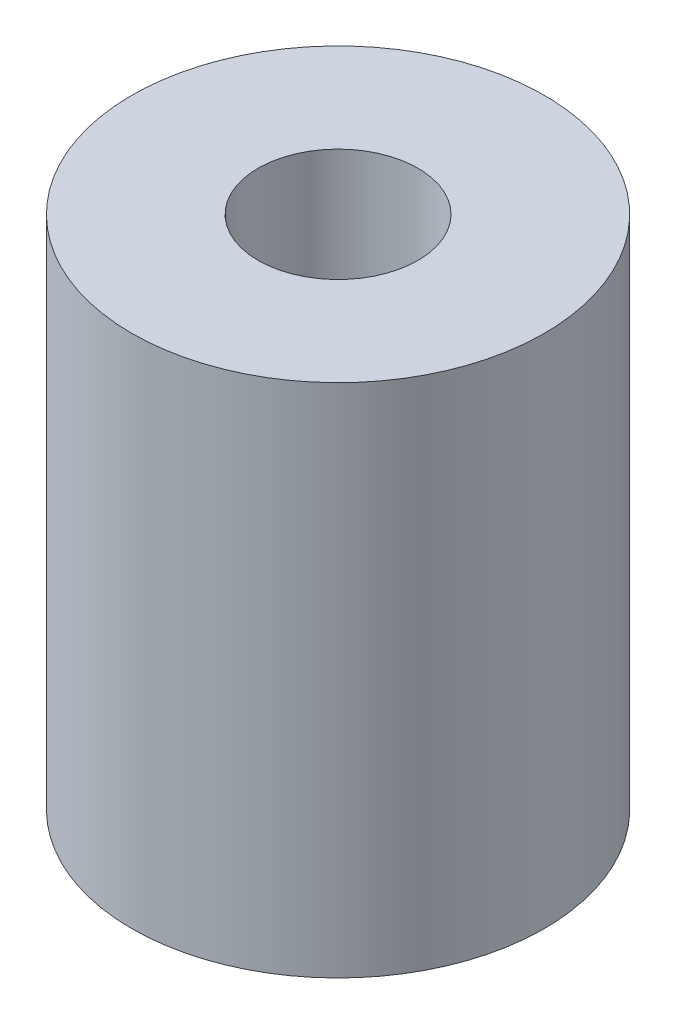
SolidWorks part; units mm, degrees
ref_plane "Front Plane" through (0, 0, 0) normal (0, 0, 1) x (1, 0, 0)
ref_plane "Top Plane" through (0, 0, 0) normal (0, 1, 0) x (1, 0, 0)
ref_plane "Right Plane" through (0, 0, 0) normal (1, 0, 0) x (0, 0, -1)
sketch "Sketch1" plane through (0, 0, 0) normal (0, 1, 0) x (1, 0, 0)
  circle A0 centre (0, 0) radius 8
extrude "Boss-Extrude1" add sketch "Sketch1" along normal blind 20
sketch "Sketch2" plane through (0, 20, 0) normal (0, 1, 0) x (1, 0, 0)
  circle A0 centre (0, 0) radius 3.1
extrude "Cut-Extrude1" cut sketch "Sketch2" against normal up to next
